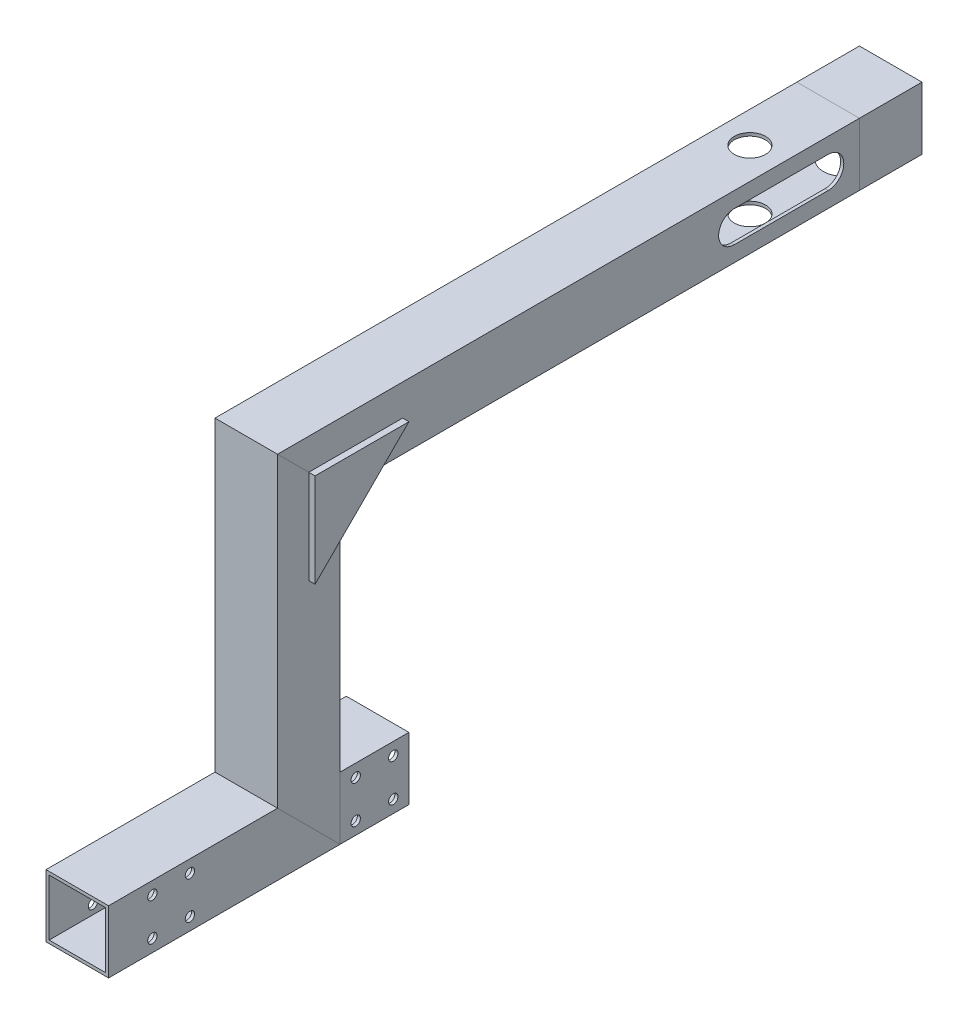
SolidWorks part; units mm, degrees
material "6063-O"
ref_plane "Front" through (0, 0, 0) normal (0, 0, 1) x (1, 0, 0)
ref_plane "Top" through (0, 0, 0) normal (0, 1, 0) x (1, 0, 0)
ref_plane "Right" through (0, 0, 0) normal (1, 0, 0) x (0, 0, -1)
sketch "草图1" plane through (0, 0, 0) normal (1, 0, 0) x (0, 0, -1)
  line L0 (0, 0) -> (64, 0)
  line L1 (64, 0) -> (64, 98)
  line L2 (64, 98) -> (240, 98)
  line L3 (64, 60) -> (4, 0) construction
  line L4 (64, 0) -> (125, 0)
  dimension "D1" = 64
  dimension "D2" = 98
  dimension "D3" = 176
  dimension "D4" = 135
  dimension "D5" = 60
  dimension "D6" = 61
other "铝管 20X20X1(1)"
ref_plane "基准面1" through (0, 0, 0) normal (0, 0, -1) x (0, 1, 0)
sketch "草图14" plane through (0, 0, 0) normal (0, 0, -1) x (0, 1, 0)
  line L1 (-10, -10) -> (10, -10)
  line L2 (-10, -10) -> (-10, 10)
  line L3 (-10, 10) -> (10, 10)
  line L4 (10, -10) -> (10, 10)
  line L5 (-10, -10) -> (10, 10) construction
  line L6 (-10, 10) -> (10, -10) construction
  line L7 (-9, -9) -> (9, -9)
  line L8 (-9, -9) -> (-9, 9)
  line L9 (-9, 9) -> (9, 9)
  line L10 (9, -9) -> (9, 9)
  line L11 (-9, -9) -> (9, 9) construction
  line L12 (-9, 9) -> (9, -9) construction
  point P0 (0, 0)
  point P6 (0, 0)
  point P11 (0, 0)
  dimension "D1" = 20
  dimension "D2" = 20
  dimension "D3" = 18
  dimension "D4" = 18
sketch "草图12" plane through (10, 0, 0) normal (1, 0, 0) x (0, 0, -1)
  line L0 (0, 0) -> (34.5882, 0) construction
  line L1 (0, 10) -> (0, -10) construction
  line L2 (6, 5) -> (34, 5) construction
  line L3 (20, 5) -> (20, -26.9272) construction
  circle A0 centre (6, 5) radius 1.5 construction
  circle A1 centre (34, 5) radius 1.5 construction
  circle A2 centre (34, -5) radius 1.5 construction
  circle A3 centre (6, -5) radius 1.5 construction
  circle A4 centre (14, 6) radius 1.5
  circle A5 centre (14, -6) radius 1.5
  circle A6 centre (26, -6) radius 1.5
  circle A7 centre (26, 6) radius 1.5
  dimension "D1" = 3
  dimension "D2" = 3
  dimension "D6" = 3
  dimension "D7" = 3
  dimension "D8" = 3
  dimension "D9" = 3
  dimension "D3" = 5
  dimension "D4" = 28
  dimension "D5" = 6
  dimension "D10" = 12
  dimension "D11" = 12
extrude "切除-拉伸1" cut sketch "草图12" against normal through all
sketch "草图15" plane through (10, 0, 0) normal (1, 0, 0) x (0, 0, -1)
  line L0 (20, 10) -> (20, -10) construction
  line L1 (54, 10) -> (0, 10) construction
  line L2 (74, -10) -> (0, -10) construction
  line L3 (0, 10) -> (0, -10) construction
  line L4 (215, 149.4201) -> (215, 66.8372) construction
  line L5 (206.1971, 98) -> (287.2027, 98) construction
  line L6 (240, 108) -> (54, 108) construction
  line L7 (200, 98) -> (230, 98) construction
  line L8 (200, 103) -> (230, 103)
  line L9 (200, 93) -> (230, 93)
  arc A0 (200, 103) -> (200, 93) centre (200, 98) ccw
  arc A1 (230, 93) -> (230, 103) centre (230, 98) ccw
  point P16 (215, 98)
  dimension "D1" = 20
  dimension "D2" = 195
  dimension "D3" = 10
  dimension "D4" = 10
  dimension "D5" = 30
extrude "切除-拉伸3" cut sketch "草图15" against normal through all
sketch "草图16" plane through (0, 88, 0) normal (0, -1, 0) x (1, 0, 0)
  line L0 (10, -230) -> (10, -200) construction
  line L1 (10, -230) -> (10, -200)
  line L2 (10, -215) -> (-10, -215) construction
  line L3 (-10, -240) -> (-10, -74) construction
  circle A0 centre (0, -215) radius 5
  dimension "D1" = 10
extrude "切除-拉伸4" cut sketch "草图16" against normal through all contours L2 A0 | A0 L2
sketch "草图17" plane through (10, 0, 0) normal (1, 0, 0) x (0, 0, -1)
  line L0 (0, 0) -> (64, 0) construction
  line L1 (54, 10) -> (74, -10) construction
  line L2 (0, 10) -> (0, -10) construction
  line L3 (74, 88) -> (74, -10) construction
  circle A0 centre (68, 6) radius 1.5 construction
  circle A1 centre (80, 6) radius 1.5 construction
  circle A2 centre (68, -6) radius 1.5 construction
  circle A3 centre (80, -6) radius 1.5 construction
  circle A4 centre (79, 6) radius 1.5
  circle A5 centre (79, -6) radius 1.5
  circle A6 centre (91, -6) radius 1.5
  circle A7 centre (91, 6) radius 1.5
  dimension "D1" = 3
  dimension "D2" = 3
  dimension "D3" = 3
  dimension "D4" = 3
  dimension "D5" = 12
  dimension "D6" = 12
  dimension "D7" = 68
  dimension "D9" = 5
  dimension "D8" = 2
ref_plane "基准面2" through (0, 98, 0) normal (0, -1, 0) x (-1, 0, 0)
sketch "草图18" [suppressed] plane through (0, 120, 0) normal (0, -1, 0) x (-1, 0, 0)
  line L0 (0, 260) -> (42.4225, 260) construction
  line L1 (10, 260) -> (40, 260)
  line L2 (10, 285) -> (10, 115) construction
  dimension "D1" = 30
other "铝管 20X20X1(12)" [suppressed]
ref_plane "基准面3" through (-10, 120, -260) normal (-1, 0, 0) x (0, 0, -1)
sketch "草图19" plane through (-10, 120, -260) normal (-1, 0, 0) x (0, 0, -1)
  line L1 (-10, -10) -> (10, -10)
  line L2 (-10, -10) -> (-10, 10)
  line L3 (-10, 10) -> (10, 10)
  line L4 (10, -10) -> (10, 10)
  line L5 (-10, -10) -> (10, 10) construction
  line L6 (-10, 10) -> (10, -10) construction
  line L7 (-9, -9) -> (9, -9)
  line L8 (-9, -9) -> (-9, 9)
  line L9 (-9, 9) -> (9, 9)
  line L10 (9, -9) -> (9, 9)
  line L11 (-9, -9) -> (9, 9) construction
  line L12 (-9, 9) -> (9, -9) construction
  point P0 (0, 0)
  point P6 (0, 0)
  point P11 (0, 0)
  dimension "D1" = 20
  dimension "D2" = 20
  dimension "D3" = 18
  dimension "D4" = 18
sketch "草图20" [suppressed] plane through (0, 110, 0) normal (0, -1, 0) x (1, 0, 0)
  line L0 (-10, -260) -> (-40, -260) construction
  line L1 (-40, -270) -> (-40, -250) construction
  circle A0 centre (-30, -260) radius 3
  dimension "D1" = 6
  dimension "D2" = 10
extrude "切除-拉伸6" [suppressed] cut sketch "草图20" against normal through all
sketch "草图22" plane through (10, 0, 0) normal (1, 0, 0) x (0, 0, -1)
  line L0 (64, 98) -> (64, 68)
  line L1 (74, 88) -> (54, 108) construction
  line L2 (64, 68) -> (94, 98)
  line L3 (94, 98) -> (64, 98)
  dimension "D1" = 30
  dimension "D2" = 45
extrude "凸台-拉伸1" add sketch "草图22" along normal blind 2 separate body
sketch "草图23" plane through (-10, 0, 0) normal (-1, 0, 0) x (0, 0, 1)
  line L3 (-64, 98) -> (-94, 98)
  line L4 (-64, 68) -> (-64, 98)
  line L5 (-94, 98) -> (-64, 68)
  line L6 (-64, 98) -> (-94, 98)
  line L7 (-64, 68) -> (-64, 98)
  line L8 (-94, 98) -> (-64, 68)
  dimension "D1" = 0
extrude "凸台-拉伸2" add sketch "草图23" along normal blind 2 separate body
sketch "草图25" plane through (0, 0, -240) normal (0, 0, -1) x (-1, 0, 0)
  line L0 (-9, 89) -> (9, 89) construction
  line L1 (9, 89) -> (9, 107) construction
  line L2 (-9, 107) -> (-9, 89) construction
  line L3 (9, 107) -> (-9, 107) construction
  line L4 (10, 108) -> (-10, 108)
  line L5 (-10, 108) -> (-10, 88)
  line L6 (-10, 88) -> (10, 88)
  line L7 (-10, 88) -> (10, 88)
  line L8 (10, 108) -> (-10, 108)
  line L9 (-10, 108) -> (-10, 88)
  line L10 (10, 88) -> (10, 108)
  line L11 (10, 88) -> (10, 108)
  line L12 (-9, 89) -> (9, 89)
  line L13 (9, 89) -> (9, 107)
  line L14 (-9, 107) -> (-9, 89)
  line L15 (9, 107) -> (-9, 107)
  dimension "D1" = 0
extrude "凸台-拉伸3" add sketch "草图25" along normal blind 20 separate body
sketch "草图26" plane through (0, 88, 0) normal (0, 1, 0) x (1, 0, 0)
  line L0 (0, 260) -> (0, 251.2186) construction
  line L1 (-10, 260) -> (10, 260) construction
  circle A0 centre (0, 245) radius 6.5
  dimension "D1" = 13
  dimension "D2" = 15
extrude "切除-拉伸9" cut sketch "草图26" along normal up to surface (1 mm away) up to face at (0, 89, -250)
sketch "草图27" plane through (0, 88, 0) normal (0, -1, 0) x (1, 0, 0)
  line L0 (6, -260) -> (6, -276.9034) construction
  line L1 (10, -260) -> (-10, -260) construction
  line L2 (10, -260) -> (10, -240) construction
  line L3 (10, -254) -> (6, -254) construction
  circle A0 centre (6, -254) radius 1.5
  dimension "D3" = 3
  dimension "D1" = 4
  dimension "D2" = 6
extrude "切除-拉伸10" cut sketch "草图27" against normal up to next (1 mm away)
extrude "切除-拉伸11" cut sketch "草图17" against normal through all
sketch "草图28" plane through (10, 0, 0) normal (1, 0, 0) x (0, 0, -1)
  line L0 (125, 10) -> (74, 10) construction
  line L1 (125, -10) -> (96, -10)
  line L2 (125, -10) -> (125, 10)
  line L3 (125, 10) -> (96, 10)
  line L4 (96, -10) -> (96, 10)
  line L5 (74, 10) -> (74, -10) construction
  dimension "D1" = 22
extrude "切除-拉伸12" cut sketch "草图28" against normal through all
